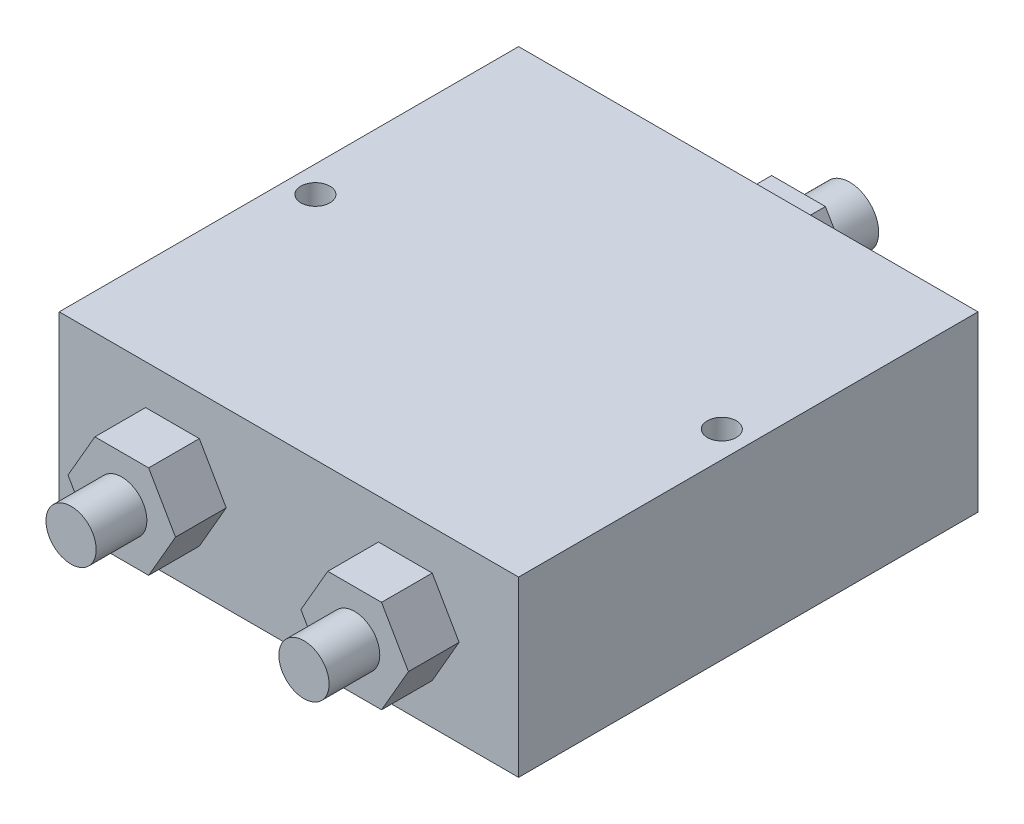
SolidWorks part; units mm, degrees
ref_plane "Front Plane" through (0, 0, 0) normal (0, 0, 1) x (1, 0, 0)
ref_plane "Top Plane" through (0, 0, 0) normal (0, 1, 0) x (1, 0, 0)
ref_plane "Right Plane" through (0, 0, 0) normal (1, 0, 0) x (0, 0, -1)
sketch "Sketch1" plane through (0, 0, 0) normal (0, 1, 0) x (1, 0, 0)
  line L1 (25.15, -25.15) -> (-25.15, -25.15)
  line L2 (25.15, -25.15) -> (25.15, 25.15)
  line L3 (25.15, 25.15) -> (-25.15, 25.15)
  line L4 (-25.15, -25.15) -> (-25.15, 25.15)
  line L5 (25.15, -25.15) -> (-25.15, 25.15) construction
  line L6 (25.15, 25.15) -> (-25.15, -25.15) construction
  point P0 (0, 0)
  dimension "D1" = 50.3
  dimension "D2" = 50.3
extrude "Boss-Extrude1" add sketch "Sketch1" along normal blind 19
sketch "Sketch2" plane through (0, 0, 25.15) normal (0, 0, 1) x (1, 0, 0)
  line L0 (-25.15, 19) -> (-25.15, 0) construction
  line L1 (-15.6929, 4.4546) -> (-9.8071, 4.4546)
  line L2 (-9.8071, 4.4546) -> (-6.8642, 9.5518)
  line L3 (-6.8642, 9.5518) -> (-9.8071, 14.649)
  line L4 (-9.8071, 14.649) -> (-15.6929, 14.649)
  line L5 (-15.6929, 14.649) -> (-18.6358, 9.5518)
  line L6 (-18.6358, 9.5518) -> (-15.6929, 4.4546)
  line L7 (0, 19) -> (0, 0)
  line L8 (-25.15, 19) -> (25.15, 19) construction
  line L9 (-25.15, 0) -> (25.15, 0) construction
  line L10 (15.6929, 4.4546) -> (9.8071, 4.4546)
  line L11 (9.8071, 4.4546) -> (6.8642, 9.5518)
  line L12 (6.8642, 9.5518) -> (9.8071, 14.649)
  line L13 (9.8071, 14.649) -> (15.6929, 14.649)
  line L14 (15.6929, 14.649) -> (18.6358, 9.5518)
  line L15 (18.6358, 9.5518) -> (15.6929, 4.4546)
  circle A0 centre (-12.75, 9.5518) radius 5.0972 construction
  circle A1 centre (12.75, 9.5518) radius 5.0972 construction
  dimension "D1" = 12.4
extrude "Boss-Extrude2" add sketch "Sketch2" along normal blind 5.55 contours L5 L6 L1 L2 L3 L4 | L15 L14 L13 L12 L11 L10
sketch "Sketch4" plane through (0, 0, -25.15) normal (0, 0, -1) x (-1, 0, 0)
  line L1 (-5.8355, 9.9844) -> (-2.8928, 4.8874)
  line L2 (-2.8928, 4.8874) -> (2.9928, 4.8874)
  line L3 (2.9928, 4.8874) -> (5.9355, 9.9844)
  line L4 (5.9355, 9.9844) -> (2.9928, 15.0814)
  line L5 (2.9928, 15.0814) -> (-2.8928, 15.0814)
  line L6 (-2.8928, 15.0814) -> (-5.8355, 9.9844)
  line L8 (25.15, 19) -> (25.15, 0) construction
  circle A0 centre (0.05, 9.9844) radius 5.097 construction
  dimension "D1" = 25.1
extrude "Boss-Extrude3" add sketch "Sketch4" along normal blind 5.55
sketch "Sketch5" plane through (0, 0, -30.7) normal (0, 0, -1) x (-1, 0, 0)
  line L1 (2.9928, 15.0814) -> (-2.8928, 15.0814) construction
  circle A0 centre (0, 9.9964) radius 3.175
  point P4 (0.05, 15.0814)
  dimension "D1" = 5.085
extrude "Boss-Extrude4" add sketch "Sketch5" along normal blind 5.55
sketch "Sketch7" plane through (0, 0, 30.7) normal (0, 0, 1) x (1, 0, 0)
  line L0 (-9.8071, 14.649) -> (-15.6929, 14.649) construction
  line L1 (0, 0) -> (0, 19.0446)
  circle A0 centre (-12.7508, 9.564) radius 2.75
  circle A1 centre (12.7508, 9.564) radius 2.75
  point P2 (-12.75, 14.649)
  dimension "D1" = 5.085
  dimension "D3" = 5.5
  dimension "D2" = 5.885
extrude "Boss-Extrude5" add sketch "Sketch7" along normal blind 5.55 contours A0 | A1
sketch "Sketch8" plane through (0, 19, 0) normal (0, 1, 0) x (1, 0, 0)
  line L0 (-25.15, 25.15) -> (-25.15, -25.15) construction
  line L1 (0, 25.15) -> (0, -25.15)
  line L2 (25.15, 25.15) -> (-25.15, 25.15) construction
  line L3 (-25.15, -25.15) -> (25.15, -25.15) construction
  circle A0 centre (-22.25, 0) radius 1.59
  circle A1 centre (22.25, 0) radius 1.59
  dimension "D1" = 2.9
extrude "Cut-Extrude1" cut sketch "Sketch8" against normal through all contours A0 | A1
